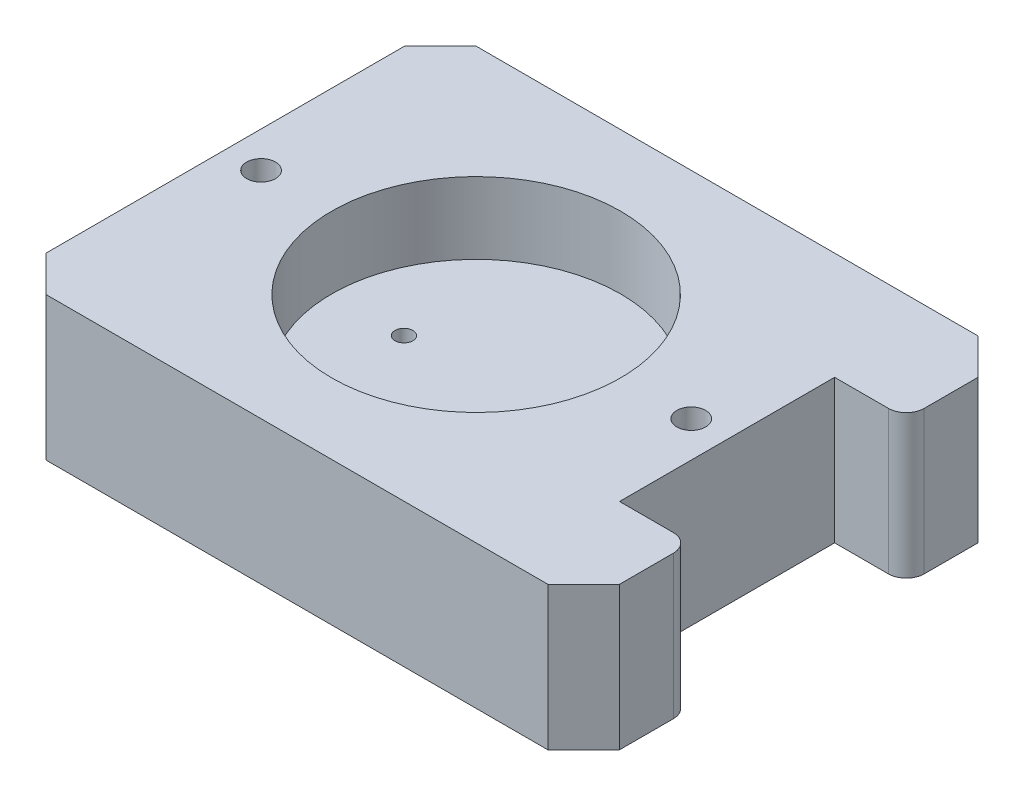
SolidWorks part; units mm, degrees
ref_plane "Front Plane" through (0, 0, 0) normal (0, 0, 1) x (1, 0, 0)
ref_plane "Top Plane" through (0, 0, 0) normal (0, 1, 0) x (1, 0, 0)
ref_plane "Right Plane" through (0, 0, 0) normal (1, 0, 0) x (0, 0, -1)
sketch "Sketch1" plane through (0, 0, 0) normal (0, 1, 0) x (1, 0, 0)
  line L0 (38.1, 0) -> (50.8, 0) construction
  line L1 (-50.8, 38.1) -> (50.8, 38.1)
  line L2 (-50.8, 38.1) -> (-50.8, -38.1)
  line L3 (-50.8, -38.1) -> (50.8, -38.1)
  line L4 (50.8, 38.1) -> (50.8, 19.05)
  line L5 (-50.8, 38.1) -> (50.8, -38.1) construction
  line L6 (-50.8, -38.1) -> (50.8, 38.1) construction
  line L7 (50.8, 19.05) -> (38.1, 19.05)
  line L9 (50.8, -19.05) -> (38.1, -19.05)
  line L10 (38.1, 19.05) -> (38.1, -19.05)
  line L11 (44.45, 38.1) -> (44.45, 0) construction
  line L12 (44.45, 0) -> (44.45, -38.1) construction
  line L13 (50.8, -19.05) -> (50.8, -38.1)
  point P0 (0, 0)
  dimension "D1" = 101.6
  dimension "D2" = 76.2
  dimension "D3" = 38.1
  dimension "D4" = 12.7
extrude "box body" add sketch "Sketch1" along normal blind 25.4
sketch "Sketch3" plane through (0, 25.4, 0) normal (0, 1, 0) x (1, 0, 0)
  line L0 (38.1, 0) -> (-6.35, 0) construction
  line L3 (38.1, -19.05) -> (38.1, 19.05) construction
  line L4 (-6.35, 0) -> (-50.8, 0) construction
  line L5 (-50.8, 38.1) -> (-50.8, -38.1) construction
  circle A0 centre (-6.35, 0) radius 25.5905
  dimension "D1" = 51.181
extrude "sample hole" cut sketch "Sketch3" against normal blind 12.7
fillet "cutout edge fillet" radius 3.175 2 edges at (50.8, 12.7, 19.05) (50.8, 12.7, -19.05)
chamfer "box edge chamfer" distance 6.35 angle 45 4 edges at (-50.8, 12.7, 38.1) (-50.8, 12.7, -38.1) (50.8, 12.7, 38.1) (50.8, 12.7, -38.1)
hole_wizard "box clamp threaded holes" positions "Sketch5" profile "Sketch4" tap size "1/4-20" standard "ANSI Inch"
sketch "Sketch5" plane through (0, 25.4, 0) normal (0, 1, 0) x (1, 0, 0)
  line L0 (38.1, 0) -> (-50.8, 0) construction
  line L1 (38.1, -19.05) -> (38.1, 19.05) construction
  line L2 (-50.8, 31.75) -> (-50.8, -31.75) construction
  circle A0 centre (-6.35, 0) radius 25.5905 construction
  point P0 (-44.45, 0)
  point P2 (31.75, 0)
  dimension "D1" = 38.1
  dimension "D2" = 38.1
sketch "Sketch4" plane through (-44.45, 25.4, 0) normal (1, 0, 0) x (0, 0, 1)
  line L0 (0, 0) -> (0, 14.2338)
  line L1 (0, 14.2338) -> (2.5527, 12.7)
  line L2 (2.5527, 12.7) -> (2.5527, 0)
  line L5 (2.5527, 0) -> (0, 0)
  line L10 (0, 14.2338) -> (-2.5527, 12.7) construction
  line L11 (0, -6.35) -> (0, 107.95) construction
  dimension "Tap Drill Dia." = 5.1054
  dimension "Tap Drill Depth" = 12.7
  dimension "Drill Angle" = 118
cosmetic thread "Hole Thread1" parameters "D1"=12.7, "D2"=6.35
cosmetic thread "Hole Thread2" parameters "D1"=12.7, "D2"=6.35
sketch "Sketch6" plane through (0, 0, 0) normal (0, 0, 1) x (1, 0, 0)
  line L0 (11.2128, 6.6593) -> (-50.8, 6.6593)
  line L1 (-50.8, 0) -> (-50.8, 25.4) construction
sketch "hole profile" plane through (-50.8, 0, 0) normal (-1, 0, 0) x (0, 0, 1)
  circle A0 centre (0, 6.4866) radius 1.7263
sweep "horizontal fluid path" [suppressed] cut profiles "hole profile" path "Sketch6"
sketch "fluid holes" plane through (0, 12.7, 0) normal (0, 1, 0) x (1, 0, 0)
  line L0 (-31.9405, 0) -> (-19.1452, 0) construction
  line L1 (-13.97, 0) -> (13.97, 0) construction
  line L2 (-19.1452, 0) -> (-6.35, 0) construction
  line L3 (-6.35, 0) -> (6.4453, 0) construction
  line L4 (6.4453, 0) -> (19.2405, 0) construction
  circle A0 centre (-6.35, 0) radius 25.5905 construction
  circle A1 centre (-19.1452, 0) radius 1.5875
  circle A2 centre (6.4453, 0) radius 1.5875
  dimension "D1" = 3.175
sketch "Sketch10" plane through (-50.8, 0, 0) normal (-1, 0, 0) x (0, 0, 1)
  line L0 (-31.75, 6.35) -> (0, 6.35) construction
  line L1 (-31.75, 25.4) -> (-31.75, 0) construction
  line L2 (0, 6.35) -> (31.75, 6.35) construction
  line L3 (31.75, 0) -> (31.75, 25.4) construction
  line L4 (41.91, 0) -> (-41.91, 0) construction
  circle A0 centre (0, 6.35) radius 1.5875
  dimension "D1" = 3.175
  dimension "D2" = 6.35
extrude "Cut-Extrude2" cut sketch "Sketch10" against normal blind 63.5 contours A0
extrude "Cut-Extrude3" cut sketch "fluid holes" against normal up to next contours A2 | A1
hole_wizard "1/16 NPT Tapped Hole1" [suppressed] positions "Sketch14" profile "Sketch13" size "1/16" standard "ANSI Inch"
sketch "Sketch14" plane through (-50.8, 0, 0) normal (-1, 0, 0) x (0, 0, 1)
  circle A0 centre (0, 6.35) radius 1.5875 construction
  point P0 (1.1167, 5.2217)
sketch "Sketch13" plane through (-50.8, 5.2217, 1.1167) normal (0, 1, 0) x (0, 0, 1)
  line L0 (0, 0) -> (0, 13.5307)
  line L1 (3.0734, 11.684) -> (0, 13.5307)
  line L2 (-3.0734, 11.684) -> (0, 13.5307) construction
  line L3 (3.0734, 11.684) -> (3.0734, 6.858)
  line L4 (3.0734, 6.858) -> (3.7626, 6.858)
  line L5 (3.7626, 6.858) -> (3.9679, 0)
  line L6 (-3.7626, 6.858) -> (-3.9679, 0) construction
  line L7 (3.9679, 0) -> (0, 0)
  line L8 (0, -6.35) -> (0, 107.95) construction
  line L11 (-3.0734, 6.858) -> (-3.7626, 6.858) construction
  dimension "Tap Drill Dia." = 6.1468
  dimension "Tap Drill Depth" = 11.684
  dimension "Thread Dia." = 7.9358
  dimension "Thread Angle" = 3.43
  dimension "Thread Depth" = 6.858
  dimension "Drill Angle" = 118
hole_wizard "1/16 NPT Tapped Hole2" positions "Sketch17" profile "Sketch15" size "1/16" standard "ANSI Inch"
sketch "Sketch17" plane through (-50.8, 0, 0) normal (-1, 0, 0) x (0, 0, 1)
  point P0 (0, 6.35)
sketch "Sketch15" plane through (-50.8, 6.35, 0) normal (0, 1, 0) x (0, 0, 1)
  line L0 (0, 0) -> (0, 13.5307)
  line L1 (3.0734, 11.684) -> (0, 13.5307)
  line L2 (-3.0734, 11.684) -> (0, 13.5307) construction
  line L3 (3.0734, 11.684) -> (3.0734, 6.858)
  line L4 (3.0734, 6.858) -> (3.7626, 6.858)
  line L5 (3.7626, 6.858) -> (3.9679, 0)
  line L6 (-3.7626, 6.858) -> (-3.9679, 0) construction
  line L7 (3.9679, 0) -> (0, 0)
  line L8 (0, -6.35) -> (0, 107.95) construction
  line L11 (-3.0734, 6.858) -> (-3.7626, 6.858) construction
  dimension "Tap Drill Dia." = 6.1468
  dimension "Tap Drill Depth" = 11.684
  dimension "Thread Dia." = 7.9358
  dimension "Thread Angle" = 3.43
  dimension "Thread Depth" = 6.858
  dimension "Drill Angle" = 118
